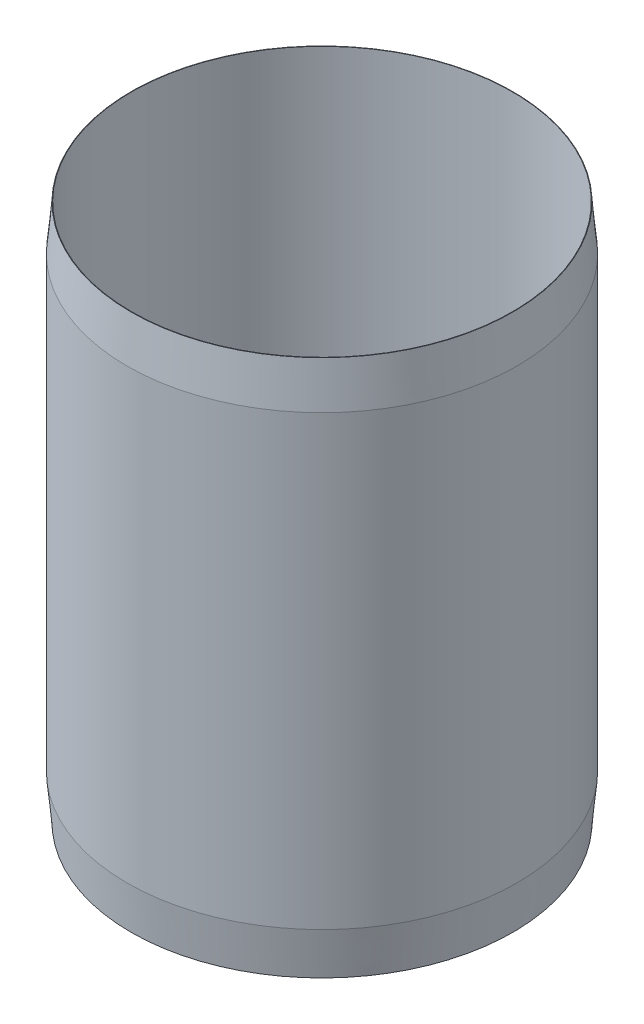
SolidWorks part; units mm, degrees
ref_plane "Front Plane" through (0, 0, 0) normal (0, 0, 1) x (1, 0, 0)
ref_plane "Top Plane" through (0, 0, 0) normal (0, 1, 0) x (1, 0, 0)
ref_plane "Right Plane" through (0, 0, 0) normal (1, 0, 0) x (0, 0, -1)
sketch "Sketch1" plane through (0, 0, 0) normal (0, 1, 0) x (1, 0, 0)
  circle A0 centre (0, 0) radius 42.55
  circle A1 centre (0, 0) radius 43.55
  dimension "D1" = 85.1
  dimension "D2" = 1
extrude "Boss-Extrude1" add sketch "Sketch1" along normal blind 120
chamfer "Chamfer1" distance 10 distance2 0.9 1 edges at (0, 120, 43.55)
chamfer "Chamfer2" distance 0.9 distance2 10 1 edges at (0, 0, 43.55)
